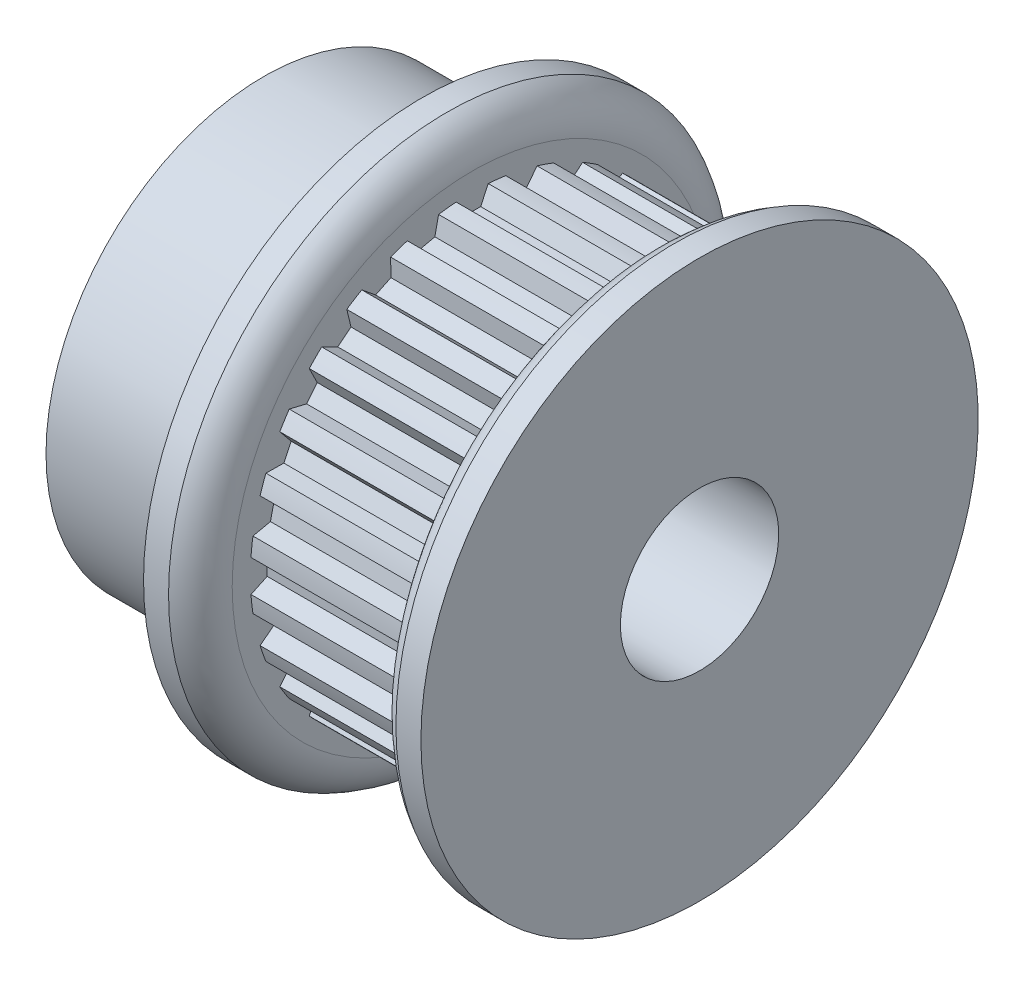
SolidWorks part; units mm, degrees
ref_plane "Front Plane" through (0, 0, 0) normal (0, 0, 1) x (1, 0, 0)
ref_plane "Top Plane" through (0, 0, 0) normal (0, 1, 0) x (1, 0, 0)
ref_plane "Right Plane" through (0, 0, 0) normal (1, 0, 0) x (0, 0, -1)
sketch "Sketch2" plane through (0, 0, 0) normal (1, 0, 0) x (0, 0, -1)
  line L3 (0, 0) -> (0, 8.2296) construction
  line L6 (0, -8.7376) -> (0, -9.0551) construction
  line L7 (-0.5715, 8.7189) -> (-0.3401, 8.2226)
  line L8 (0.5715, 8.7189) -> (0.3401, 8.2226)
  line L9 (-0.5715, 8.7189) -> (-0.6434, 8.8731)
  line L10 (0.5715, 8.7189) -> (0.6434, 8.8731)
  line L12 (-0.3401, 8.2226) -> (0.3401, 8.2226)
  line L14 (0, 8.7376) -> (0, 9.0551) construction
  line L15 (0, 0) -> (0, -1.143) construction
  circle A0 centre (0, 0) radius 9.0551 construction
  circle A1 centre (0, 0) radius 8.2296 construction
  circle A2 centre (0, 0) radius 8.7376 construction
  arc A7 (0.6434, 8.8731) -> (-0.6434, 8.8731) centre (0, 0) ccw
  point P5 (0, 8.8963)
  dimension "D3" = 0.3175
  dimension "D1" = 50
sketch "Sketch1" plane through (0, 0, 0) normal (0, 0, 1) x (1, 0, 0)
  line L0 (-8.7376, 0) -> (8.7376, 0) construction
  line L1 (-8.7376, 3.175) -> (8.7376, 3.175)
  line L2 (-8.7376, 3.175) -> (-8.7376, 8.7376)
  line L3 (-2.3876, 11.176) -> (-1.3843, 11.176)
  line L4 (-0.381, 9.0551) -> (-0.381, 9.6266)
  line L5 (-0.381, 10.1981) -> (-0.381, 9.0551) construction
  line L6 (-0.381, 9.0551) -> (6.731, 9.0551)
  line L7 (6.731, 9.0551) -> (6.731, 9.6266)
  line L8 (6.731, 9.0551) -> (8.7376, 9.0551) construction
  line L9 (7.7343, 11.176) -> (8.7376, 11.176)
  line L10 (8.7376, 11.176) -> (8.7376, 3.175)
  line L11 (7.7343, 9.0551) -> (7.7343, 11.176) construction
  line L12 (-5.5626, 8.7376) -> (-5.5626, 3.175) construction
  line L13 (-2.3876, 11.176) -> (-2.3876, 8.7376)
  line L14 (-2.3876, 8.7376) -> (-8.7376, 8.7376)
  arc A0 (6.731, 9.6266) -> (7.7343, 11.176) centre (8.429, 9.6266) cw
  arc A1 (-0.381, 9.6266) -> (-1.3843, 11.176) centre (-2.079, 9.6266) ccw
  dimension "Bore Size" = 6.35
  dimension "Overall Width" = 17.4752
  dimension "Inside Width" = 7.112
  dimension "OD" = 22.352
  dimension "D2" = 18.1102
  dimension "D3" = 1.143
  dimension "D4" = 0.5715
  dimension "Outside Width" = 11.1252
revolve "Revolve1" add sketch "Sketch1" angle 360 mid plane about L0
sketch "Sketch4" plane through (-0.381, 0, 0) normal (1, 0, 0) x (0, 0, -1)
  circle A0 centre (0, 0) radius 8.8963
  circle A2 centre (0, 0) radius 9.0551
  circle A3 centre (0, 0) radius 9.0551 construction
extrude "Cut-Extrude2" cut sketch "Sketch4" along normal up to surface (7.112 mm away) up to face at (6.731, 0, 9.0551)
sketch "Sketch3" plane through (-0.381, 0, 0) normal (1, 0, 0) x (0, 0, -1)
  line L2 (-0.5715, 8.7189) -> (-0.3401, 8.2226) construction
  line L3 (-0.3401, 8.2226) -> (0.3401, 8.2226) construction
  line L4 (0.5715, 8.7189) -> (0.3401, 8.2226) construction
  line L5 (-0.6434, 8.8731) -> (-0.3401, 8.2226)
  line L6 (-0.3401, 8.2226) -> (0.3401, 8.2226)
  line L7 (0.6434, 8.8731) -> (0.3401, 8.2226)
  arc A1 (0.6434, 8.8731) -> (-0.6434, 8.8731) centre (0, 0) ccw construction
  arc A2 (0.6434, 8.8731) -> (-0.6434, 8.8731) centre (0, 0) ccw
extrude "Cut-Extrude1" cut sketch "Sketch3" along normal up to surface (7.112 mm away) up to face at (6.731, 0, 9.6266)
pattern_circular "CirPattern1" count 28 over 360 about axis through (0, 0, 0) along (1, 0, 0) of "Cut-Extrude1"
sketch "Sketch5" plane through (0, 0, 0) normal (0, 0, 1) x (1, 0, 0)
  line L1 (6.731, 9.6266) -> (6.731, -9.6266) construction
  point P0 (6.731, 0)
equation "\"D3@Sketch2\" = (\"hs@Sketch2\"-\"ht@Sketch2\")/2"
equation "\"D2@Sketch1\" = \"PD@Sketch2\""
equation "\"D3@Sketch1\" = \"hs@Sketch2\""
equation "\"D4@Sketch1\" = \"D3@Sketch1\"/2"
